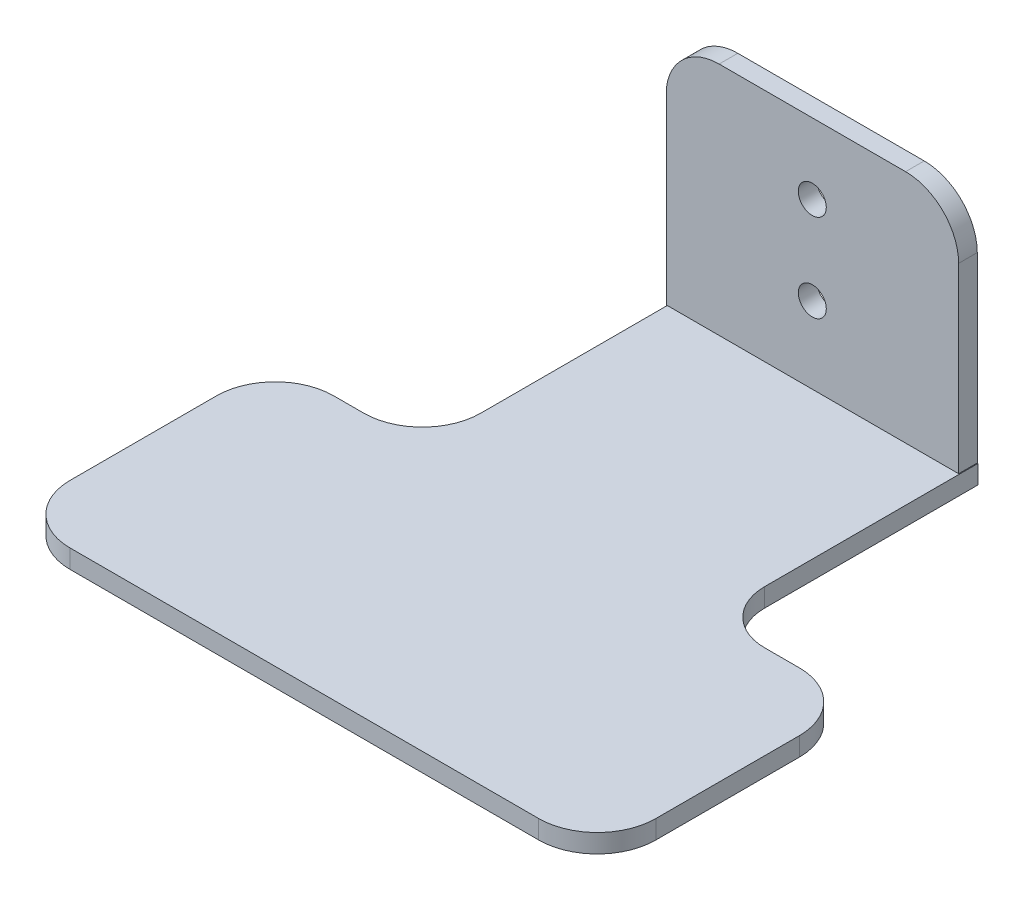
SolidWorks part; units mm, degrees
ref_plane "Front Plane" through (0, 0, 0) normal (0, 0, 1) x (1, 0, 0)
ref_plane "Top Plane" through (0, 0, 0) normal (0, 1, 0) x (1, 0, 0)
ref_plane "Right Plane" through (0, 0, 0) normal (1, 0, 0) x (0, 0, -1)
sketch "Sketch2" plane through (0, 0, 0) normal (0, 1, 0) x (1, 0, 0)
  line L0 (41.1331, -45.4773) -> (47.0747, -45.4773)
  line L1 (57.0747, -55.4773) -> (57.0747, -80.0061)
  line L2 (47.0747, -90.0061) -> (-32.9253, -90.0061)
  line L3 (-42.9253, -80.0061) -> (-42.9253, -55.0061)
  line L4 (-32.9253, -45.0061) -> (-27.8002, -45.0061)
  line L5 (-17.8002, -35.0061) -> (-17.8002, -0.0061)
  line L6 (-17.8002, -0.0061) -> (32.0747, -0.0061)
  line L7 (32.0747, -0.0061) -> (32.0747, -36.4189)
  circle A0 centre (-17.9253, -67.5061) radius 5
  circle A2 centre (32.0747, -67.5061) radius 5
  arc A3 (47.0747, -90.0061) -> (57.0747, -80.0061) centre (47.0747, -80.0061) ccw
  arc A4 (57.0747, -55.4773) -> (47.0747, -45.4773) centre (47.0747, -55.4773) ccw
  arc A5 (-32.9253, -90.0061) -> (-42.9253, -80.0061) centre (-32.9253, -80.0061) cw
  arc A6 (-32.9253, -45.0061) -> (-42.9253, -55.0061) centre (-32.9253, -55.0061) ccw
  arc A7 (-17.8002, -35.0061) -> (-27.8002, -45.0061) centre (-27.8002, -35.0061) cw
  arc A8 (41.1331, -45.4773) -> (32.0747, -36.4189) centre (41.1331, -36.4189) cw
  point P12 (57.0747, -90.0061)
  point P17 (-42.9253, -90.0061)
  point P20 (-42.9253, -45.0061)
  dimension "D1" = 10
  dimension "D4" = 10
  dimension "D5" = 25
  dimension "D8" = 10
  dimension "D10" = 10
  dimension "D11" = 9.0584
  dimension "0.01" = 100
  dimension "D2" = 45
  dimension "D3" = 22.5
  dimension "D6" = 25
  dimension "D7" = 50
  dimension "D9" = 90
sketch "Sketch4" plane through (0, 0, 0) normal (0, 0, 1) x (1, 0, 0)
  line L0 (-17.9253, 35.4196) -> (-17.9253, 0.3495)
  line L2 (-8.9423, 43.3112) -> (22.8863, 43.3112)
  line L3 (-17.9253, 0.3495) -> (31.9446, 0.3495)
  line L5 (-8.9423, 34.2527) -> (-8.9423, 28.2527) construction
  line L6 (-6.9457, 34.2527) -> (-6.9457, 28.2527) construction
  line L7 (-10.939, 34.2527) -> (-10.939, 28.2527) construction
  line L8 (-8.9423, 19.2527) -> (-8.9423, 13.2527) construction
  line L11 (-6.8735, 19.2527) -> (-6.8735, 13.2527) construction
  line L12 (-11.0112, 19.2527) -> (-11.0112, 13.2527) construction
  line L13 (31.9446, 0.3495) -> (31.9446, 34.2871)
  circle A0 centre (6.9581, 31.2527) radius 2.39
  circle A1 centre (6.9581, 16.2527) radius 2.39
  arc A2 (31.9446, 34.2871) -> (22.8863, 43.3112) centre (22.8863, 34.2527) ccw
  arc A3 (-8.9423, 43.3112) -> (-17.9253, 35.4196) centre (-8.9423, 34.2527) ccw
  arc A4 (-6.9457, 34.2527) -> (-10.939, 34.2527) centre (-8.9423, 34.2527) ccw construction
  arc A5 (-10.939, 28.2527) -> (-6.9457, 28.2527) centre (-8.9423, 28.2527) ccw construction
  arc A8 (-6.8735, 19.2527) -> (-11.0112, 19.2527) centre (-8.9423, 19.2527) ccw construction
  arc A9 (-11.0112, 13.2527) -> (-6.8735, 13.2527) centre (-8.9423, 13.2527) ccw construction
  point P17 (-8.9423, 31.2527)
  point P24 (-8.9423, 16.2527)
  dimension "D1" = 4.78
  dimension "D2" = 4.78
  dimension "D3" = 15
  dimension "D4" = 9.0584
  dimension "D5" = 6
  dimension "D6" = 6
extrude "Boss-Extrude4" add sketch "Sketch4" along normal blind 3.18
extrude "Boss-Extrude5" add sketch "Sketch2" along normal blind 3.18 contours L5 L6 L7 A8 L0 A4 L1 A3 L2 A5 L3 A6 L4 A7
